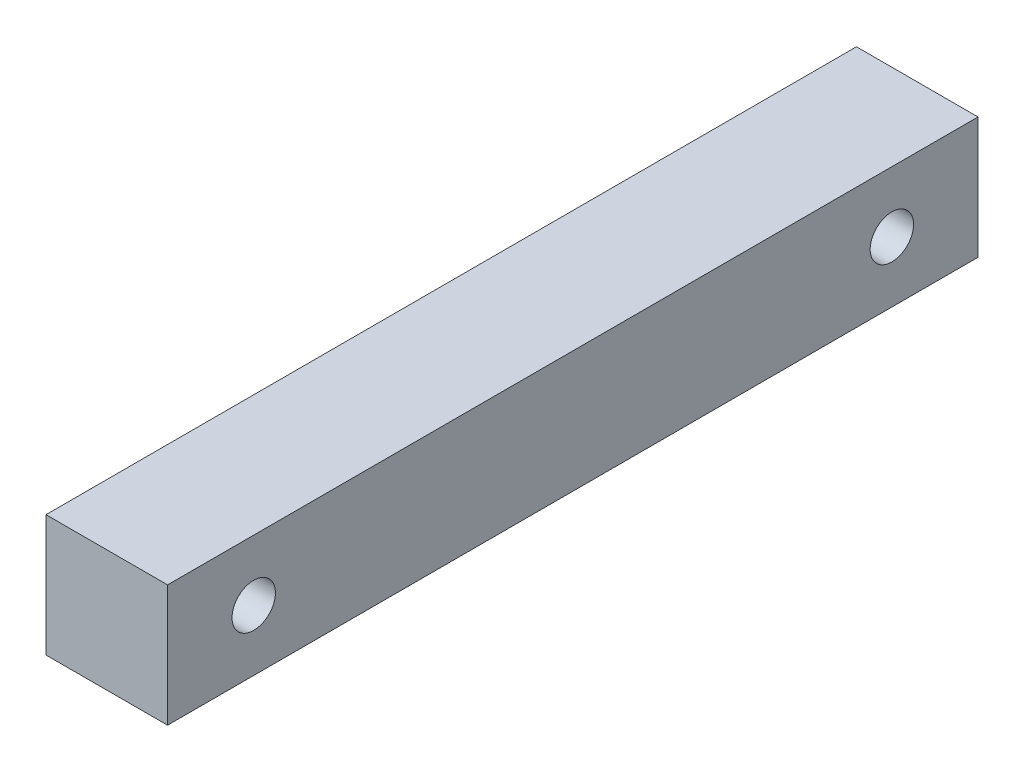
SolidWorks part; units mm, degrees
material "AISI 1020"
ref_plane "Frontal" through (0, 0, 0) normal (0, 0, 1) x (1, 0, 0)
ref_plane "Superior" through (0, 0, 0) normal (0, 1, 0) x (1, 0, 0)
ref_plane "Direito" through (0, 0, 0) normal (1, 0, 0) x (0, 0, -1)
sketch "Esboço1" plane through (0, 0, 0) normal (0, 0, 1) x (1, 0, 0)
  line L1 (-9.525, -9.525) -> (9.525, -9.525)
  line L2 (-9.525, -9.525) -> (-9.525, 9.525)
  line L3 (-9.525, 9.525) -> (9.525, 9.525)
  line L4 (9.525, -9.525) -> (9.525, 9.525)
  line L5 (-9.525, -9.525) -> (9.525, 9.525) construction
  line L6 (-9.525, 9.525) -> (9.525, -9.525) construction
  point P0 (0, 0)
  dimension "D1" = 19.05
extrude "Ressalto-extrusão1" add sketch "Esboço1" along normal mid plane 127
sketch "Esboço2" plane through (9.525, 0, 0) normal (1, 0, 0) x (0, 0, -1)
  line L0 (50, 0) -> (-50, 0) construction
  point P0 (-50, 0)
  point P1 (50, 0)
  point P5 (0, 0)
  dimension "D1" = 100
hole_wizard "Furo roscado de M81" positions "Esboço4" profile "Esboço5" tap size "M8" standard "DIN" end condition through all
sketch "Esboço4" plane through (9.525, 0, 0) normal (1, 0, 0) x (0, 0, -1)
  point P0 (-50, 0)
  point P3 (50, 0)
sketch "Esboço5" plane through (9.525, 0, 50) normal (0, 1, 0) x (0, 0, -1)
  line L0 (0, 0) -> (0, 19.05)
  line L1 (0, 19.05) -> (3.4, 19.05)
  line L2 (3.4, 19.05) -> (3.4, 0)
  line L5 (3.4, 0) -> (0, 0)
  line L11 (0, -6.35) -> (0, 107.95) construction
  dimension "Thru Tap Drill Dia." = 6.8
  dimension "Thru Tap Drill Depth" = 19.05
cosmetic thread "Rosca de furo1" parameters "D1"=16, "D2"=8
cosmetic thread "Rosca de furo2" parameters "D1"=16, "D2"=8
